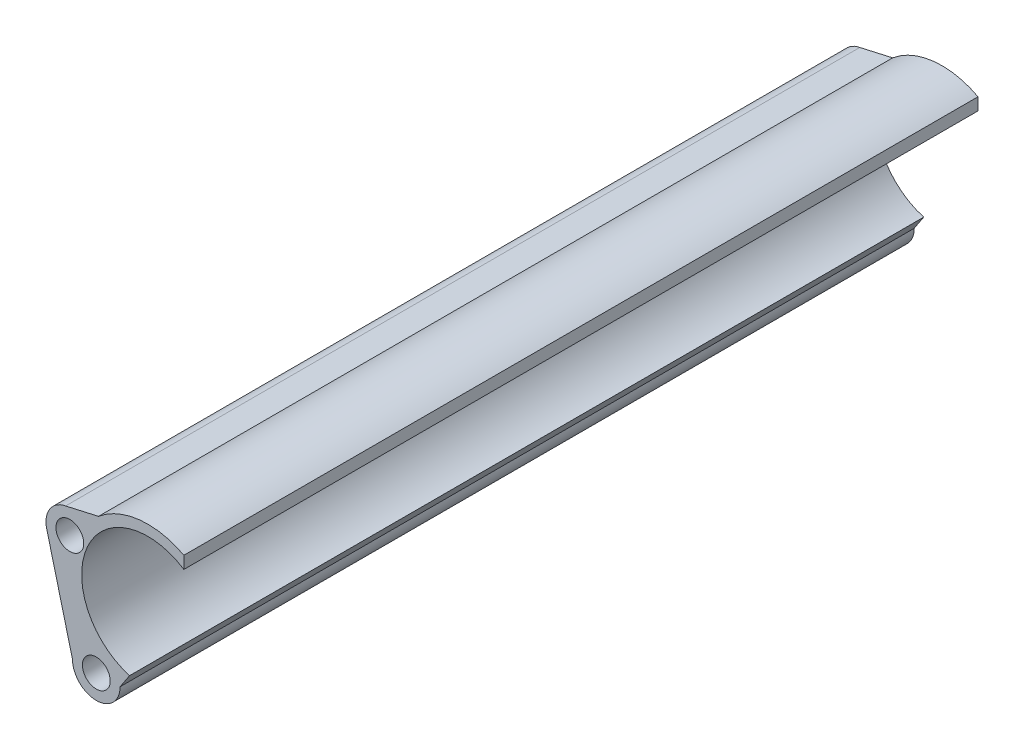
SolidWorks part; units mm, degrees
ref_plane "Plan de face" through (0, 0, 0) normal (0, 0, 1) x (1, 0, 0)
ref_plane "Plan de dessus" through (0, 0, 0) normal (0, 1, 0) x (1, 0, 0)
ref_plane "Plan de droite" through (0, 0, 0) normal (1, 0, 0) x (0, 0, -1)
sketch "Esquisse1" plane through (0, 0, 0) normal (0, 0, 1) x (1, 0, 0)
  line L0 (-4.358, -1.1215) -> (0.5, -20)
  line L8 (5.4196, 5.8362) -> (-0.7976, 4.4288)
  line L9 (10.5992, -17.0688) -> (11.5992, -16.8114)
  line L10 (11.5992, -16.8114) -> (9.5, -20)
  line L12 (21.5407, 7.5313) -> (21.5407, 5.2128)
  circle A0 centre (0, 0) radius 2.625
  circle A1 centre (5, -20) radius 2.625
  arc A3 (0.5, -20) -> (9.5, -20) centre (5, -20) ccw
  arc A4 (-0.7976, 4.4288) -> (-4.358, -1.1215) centre (0, 0) ccw
  arc A5 (10.3767, 6.4411) -> (10.5992, -17.0688) centre (14.7374, -5.2736) ccw
  arc A6 (21.5407, 5.2128) -> (11.2857, -17.2876) centre (14.7374, -5.2736) ccw
  arc A7 (21.5407, 7.5313) -> (5.4196, 5.8362) centre (14.7374, -5.2736) ccw
  dimension "D1" = 5.25
  dimension "D2" = 5.25
  dimension "D5" = 25
  dimension "D6" = 9
  dimension "D10" = 29
  dimension "D3" = 5
  dimension "D4" = 20
  dimension "D7" = 5.5992
  dimension "D8" = 2.9312
  dimension "D9" = 1
extrude "Boss.-Extru.1" add sketch "Esquisse1" along normal blind 150
